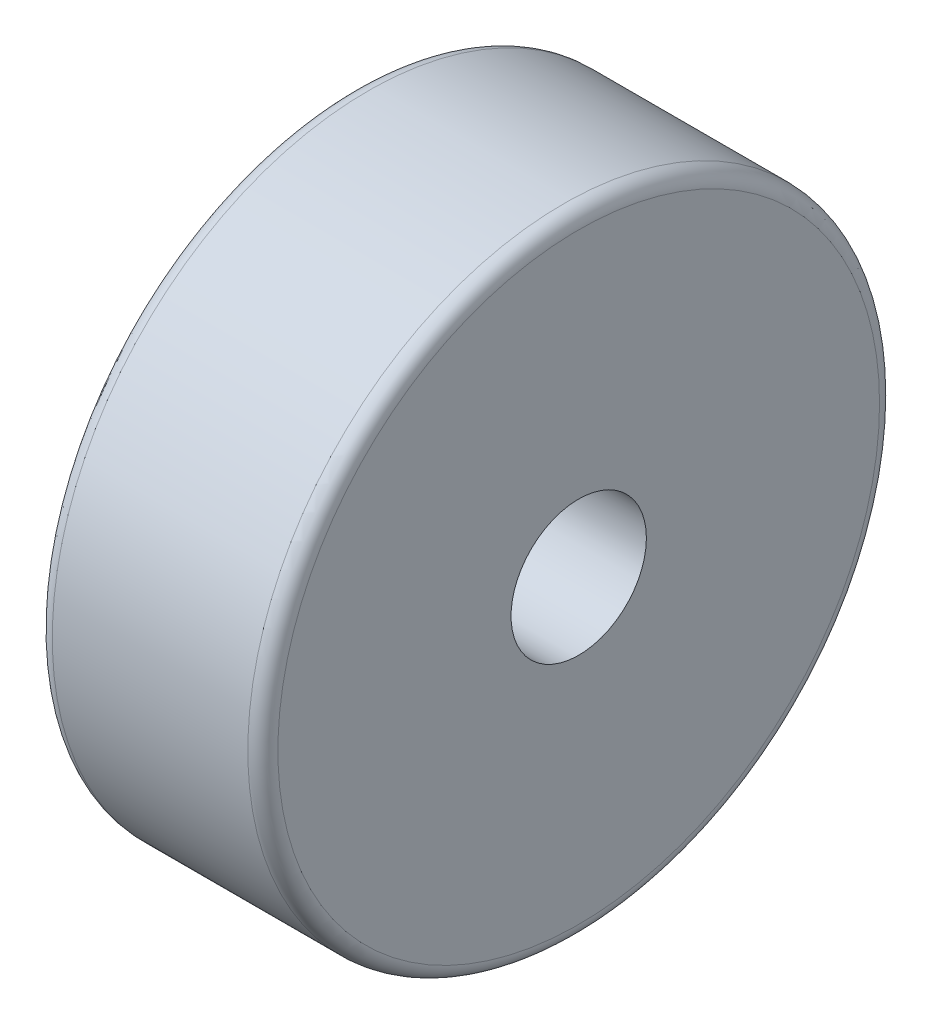
SolidWorks part; units mm, degrees
ref_plane "Front Plane" through (0, 0, 0) normal (0, 0, 1) x (1, 0, 0)
ref_plane "Top Plane" through (0, 0, 0) normal (0, 1, 0) x (1, 0, 0)
ref_plane "Right Plane" through (0, 0, 0) normal (1, 0, 0) x (0, 0, -1)
sketch "Sketch1" plane through (0, 0, 0) normal (1, 0, 0) x (0, 0, -1)
  circle A0 centre (0, 0) radius 21
  dimension "D1" = 42
extrude "Boss-Extrude1" add sketch "Sketch1" against normal blind 15
fillet "Fillet1" radius 1 2 edges at (-15, 0, -21) (0, 0, -21)
sketch "Sketch2" plane through (0, 0, 0) normal (1, 0, 0) x (0, 0, -1)
  circle A0 centre (0, 0) radius 4.5
  dimension "D1" = 9
extrude "Cut-Extrude1" cut sketch "Sketch2" against normal blind 15
